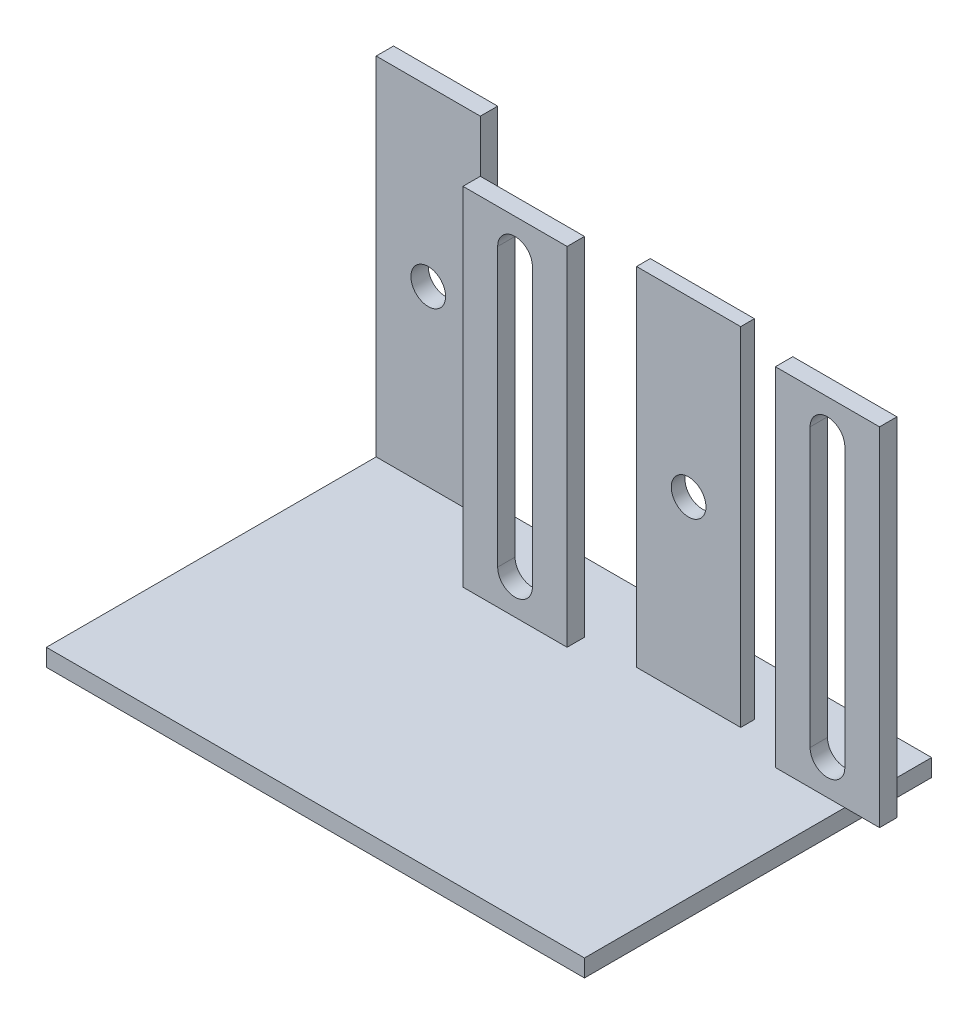
SolidWorks part; units mm, degrees
ref_plane "Front Plane" through (0, 0, 0) normal (0, 0, 1) x (1, 0, 0)
ref_plane "Top Plane" through (0, 0, 0) normal (0, 1, 0) x (1, 0, 0)
ref_plane "Right Plane" through (0, 0, 0) normal (1, 0, 0) x (0, 0, -1)
sketch "Sketch1" plane through (0, 0, 0) normal (0, 1, 0) x (1, 0, 0)
  line L1 (0, 0) -> (310, 0)
  line L2 (0, 0) -> (0, 200)
  line L3 (0, 200) -> (310, 200)
  line L4 (310, 0) -> (310, 200)
  dimension "D1" = 310
  dimension "D2" = 200
extrude "Boss-Extrude1" add sketch "Sketch1" along normal blind 10
sketch "Sketch2" plane through (0, 10, 0) normal (0, 1, 0) x (1, 0, 0)
  line L0 (310, 200) -> (0, 200) construction
  line L1 (0, 200) -> (60, 200)
  line L2 (0, 200) -> (0, 190)
  line L3 (0, 190) -> (60, 190)
  line L4 (60, 200) -> (60, 190)
  line L5 (90, 160) -> (150, 160)
  line L6 (90, 160) -> (90, 150)
  line L7 (90, 150) -> (150, 150)
  line L8 (150, 160) -> (150, 150)
  line L9 (270, 160) -> (330, 160)
  line L10 (270, 160) -> (270, 150)
  line L11 (270, 150) -> (330, 150)
  line L12 (330, 160) -> (330, 150)
  line L14 (180, 160) -> (240, 160)
  line L15 (180, 160) -> (180, 167.9129)
  line L16 (180, 167.9129) -> (240, 167.9129)
  line L17 (240, 160) -> (240, 167.9129)
  dimension "D1" = 60
  dimension "D2" = 10
  dimension "D3" = 60
  dimension "D4" = 10
  dimension "D5" = 60
  dimension "D6" = 10
  dimension "D7" = 120
  dimension "D8" = 50
  dimension "D9" = 30
  dimension "D10" = 60
  dimension "D11" = 30
extrude "Boss-Extrude2" add sketch "Sketch2" along normal blind 200
sketch "Sketch3" plane through (0, 0, -150) normal (0, 0, 1) x (1, 0, 0)
  line L0 (120, 210) -> (120, 10) construction
  line L1 (90, 210) -> (150, 210) construction
  line L2 (90, 10) -> (150, 10) construction
  line L3 (300, 210) -> (300, 10) construction
  line L6 (30, 210) -> (30, 10) construction
  line L7 (0, 210) -> (60, 210) construction
  line L8 (0, 10) -> (60, 10) construction
  line L9 (110, 190) -> (110, 30)
  line L11 (130, 30) -> (130, 190)
  line L12 (290, 190) -> (290, 30)
  line L13 (210, 210) -> (210, 10) construction
  line L14 (310, 30) -> (310, 190)
  line L15 (180, 210) -> (240, 210) construction
  line L16 (180, 10) -> (240, 10) construction
  line L17 (270, 210) -> (330, 210) construction
  line L18 (270, 10) -> (310, 10) construction
  circle A0 centre (30, 110) radius 10
  arc A1 (130, 190) -> (110, 190) centre (120, 190) ccw
  arc A2 (110, 30) -> (130, 30) centre (120, 30) ccw
  arc A3 (310, 190) -> (290, 190) centre (300, 190) ccw
  arc A4 (290, 30) -> (310, 30) centre (300, 30) ccw
  circle A5 centre (210, 110) radius 10
  point P40 (300, 190)
  point P41 (300, 28.4587)
  dimension "D1" = 20
  dimension "D2" = 20
  dimension "D4" = 20
  dimension "D6" = 20
  dimension "D8" = 20
  dimension "D10" = 20
  dimension "D3" = 20
  dimension "D5" = 20
  dimension "D7" = 20
  dimension "D9" = 20
extrude "Cut-Extrude1" cut sketch "Sketch3" against normal blind 200
